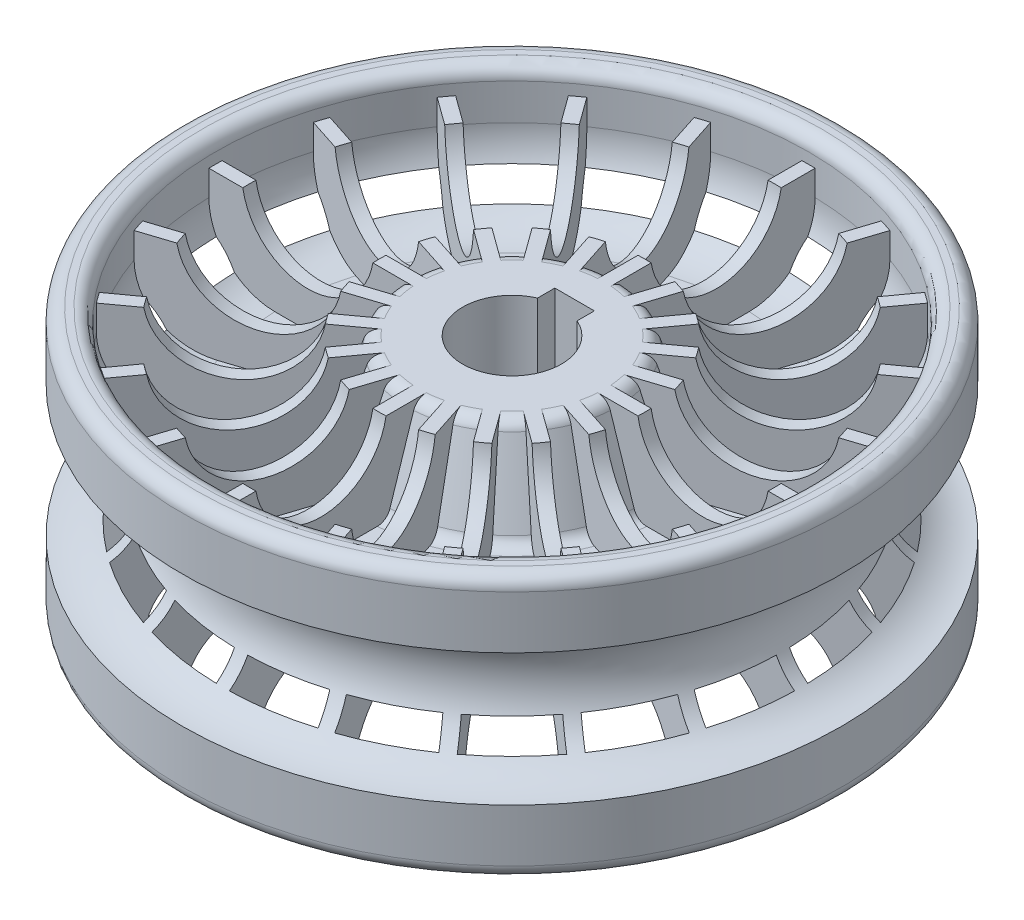
SolidWorks part; units mm, degrees
ref_plane "Front Plane" through (0, 0, 0) normal (0, 0, 1) x (1, 0, 0)
ref_plane "Top Plane" through (0, 0, 0) normal (0, 1, 0) x (1, 0, 0)
ref_plane "Right Plane" through (0, 0, 0) normal (1, 0, 0) x (0, 0, -1)
sketch "Sketch1" plane through (0, 0, 0) normal (0, 0, 1) x (1, 0, 0)
  line L0 (0, 0) -> (0, 10.403) construction
  line L1 (0, 0) -> (-12.0005, 0) construction
  line L2 (-3.75, -8.1748) -> (-3.75, 8.1748)
  line L3 (-3.75, 8.1748) -> (-7.75, 8.1748)
  line L4 (-7.75, 8.1748) -> (-10, 1.25)
  line L5 (-10, 1.25) -> (-22.5, 1.25)
  line L6 (-22.5, 1.25) -> (-22.5, 10)
  line L7 (-22.5, 10) -> (-25, 10)
  line L8 (-25, 10) -> (-25, -10)
  line L10 (-3.75, -8.1748) -> (-7.75, -8.1748)
  line L11 (-7.75, -8.1748) -> (-10, -1.25)
  line L12 (-10, -1.25) -> (-22.5, -1.25)
  line L13 (-22.5, -1.25) -> (-22.5, -10)
  line L14 (-22.5, -10) -> (-25, -10)
  point P6 (0, 0)
  point P14 (-3.75, 0)
  point P19 (-25, 0)
  dimension "D1" = 20
  dimension "D2" = 2.5
  dimension "D3" = 7.5
  dimension "D4" = 50
  dimension "D5" = 2.5
  dimension "D6" = 20
  dimension "D7" = 4
  dimension "D8" = 18
revolve "Revolve1" add sketch "Sketch1" angle 360 about L0
fillet "Fillet1" radius 1 8 edges at (0, -1.25, -10) (0, -8.1748, -7.75) (0, 8.1748, -7.75) (0, 1.25, -10) (0, 10, -22.5) (0, 10, -25) (0, -10, -22.5) (0, -10, -25)
fillet "Fillet2" radius 5 2 edges at (0, -1.25, -22.5) (0, 1.25, -22.5)
sketch "Sketch2" plane through (0, 8.1748, 0) normal (0, 1, 0) x (1, 0, 0)
  line L0 (0, 10.7265) -> (0, 17.5)
  circle A0 centre (0, 0) radius 10.7265 construction
  circle A1 centre (0, 0) radius 17.5 construction
rib "Rib5" sketch "Sketch2" sketch "Sketch2" thickness 1 extrusion direction normal to sketch draft on no parameters "D1"=1
mirror "Mirror1" about plane through (0, 0, 0) normal (0, 1, 0) of "Rib5"
pattern_circular "CirPattern1" count 20 over 360 about axis through (0, 0, 0) along (0, 1, 0) of "Mirror1", "Rib5"
sketch "Sketch3" plane through (0, 0, 0) normal (0, 0, 1) x (1, 0, 0)
  line L0 (0, 0) -> (0, 17.1129) construction
  line L1 (0, 0) -> (-25, 0) construction
  line L2 (-25, 9) -> (-25, -9) construction
  line L3 (25, 9) -> (-25, 9) construction
  circle A0 centre (-25, 0) radius 5
  circle A1 centre (-15, 9) radius 5
  circle A2 centre (-15, -9) radius 5
  dimension "D1" = 10
  dimension "D2" = 30
revolve "Cut-Revolve1" cut sketch "Sketch3" angle 360 about L0
sketch "Sketch4" plane through (0, 8.1748, 0) normal (0, 1, 0) x (1, 0, 0)
  line L1 (1.5, 2.75) -> (-1.5, 2.75)
  line L2 (1.5, 2.75) -> (1.5, 4.75)
  line L3 (1.5, 4.75) -> (-1.5, 4.75)
  line L4 (-1.5, 2.75) -> (-1.5, 4.75)
  line L5 (1.5, 2.75) -> (-1.5, 4.75) construction
  line L6 (1.5, 4.75) -> (-1.5, 2.75) construction
  circle A0 centre (0, 0) radius 3.75 construction
  point P0 (0, 3.75)
  dimension "D1" = 2
  dimension "D2" = 3
extrude "Cut-Extrude2" cut sketch "Sketch4" against normal through all both and the other way through all
